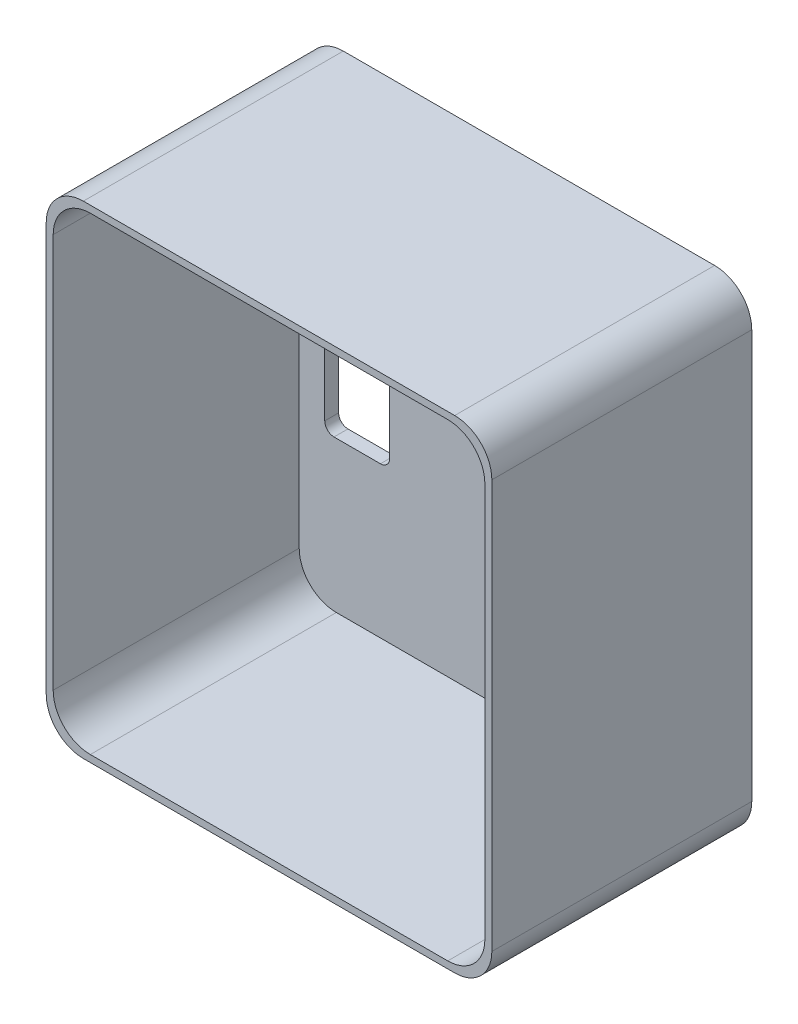
SolidWorks part; units mm, degrees
ref_plane "Front Plane" through (0, 0, 0) normal (0, 0, 1) x (1, 0, 0)
ref_plane "Top Plane" through (0, 0, 0) normal (0, 1, 0) x (1, 0, 0)
ref_plane "Right Plane" through (0, 0, 0) normal (1, 0, 0) x (0, 0, -1)
sketch "Sketch1" plane through (0, 0, 0) normal (0, 0, 1) x (1, 0, 0)
  line L1 (-20, 26) -> (20, 26)
  line L2 (-24, 22) -> (-24, -22)
  line L3 (-20, -26) -> (20, -26)
  line L4 (24, 22) -> (24, -22)
  line L5 (-24, 26) -> (24, -26) construction
  line L6 (-24, -26) -> (24, 26) construction
  arc A0 (20, -26) -> (24, -22) centre (20, -22) ccw
  arc A1 (-24, -22) -> (-20, -26) centre (-20, -22) ccw
  arc A2 (24, 22) -> (20, 26) centre (20, 22) ccw
  arc A3 (-20, 26) -> (-24, 22) centre (-20, 22) ccw
  point P0 (0, 0)
  dimension "D3" = 4
  dimension "D1" = 52
  dimension "D2" = 48
extrude "Boss-Extrude1" add sketch "Sketch1" along normal blind 28
sketch "Sketch2" plane through (0, 0, 28) normal (0, 0, 1) x (1, 0, 0)
  line L1 (-19.25, 25.25) -> (19.25, 25.25)
  line L2 (-23.25, 21.25) -> (-23.25, -21.25)
  line L3 (-19.25, -25.25) -> (19.25, -25.25)
  line L4 (23.25, 21.25) -> (23.25, -21.25)
  line L5 (-23.25, 25.25) -> (23.25, -25.25) construction
  line L6 (-23.25, -25.25) -> (23.25, 25.25) construction
  arc A0 (-23.25, -21.25) -> (-19.25, -25.25) centre (-19.25, -21.25) ccw
  arc A1 (19.25, -25.25) -> (23.25, -21.25) centre (19.25, -21.25) ccw
  arc A2 (23.25, 21.25) -> (19.25, 25.25) centre (19.25, 21.25) ccw
  arc A3 (-19.25, 25.25) -> (-23.25, 21.25) centre (-19.25, 21.25) ccw
  point P0 (0, 0)
  dimension "D3" = 4
  dimension "D1" = 50.5
  dimension "D2" = 46.5
extrude "Cut-Extrude1" cut sketch "Sketch2" against normal blind 26.5
sketch "Sketch3" plane through (0, 0, 1.5) normal (0, 0, 1) x (1, 0, 0)
  line L1 (-19.5, 9) -> (-14.5, 9)
  line L2 (-20.5, 8) -> (-20.5, -8)
  line L3 (-19.5, -9) -> (-14.5, -9)
  line L4 (-13.5, 8) -> (-13.5, -8)
  line L5 (-20.5, 9) -> (-13.5, -9) construction
  line L6 (-20.5, -9) -> (-13.5, 9) construction
  arc A0 (-20.5, -8) -> (-19.5, -9) centre (-19.5, -8) ccw
  arc A1 (-14.5, -9) -> (-13.5, -8) centre (-14.5, -8) ccw
  arc A2 (-13.5, 8) -> (-14.5, 9) centre (-14.5, 8) ccw
  arc A3 (-19.5, 9) -> (-20.5, 8) centre (-19.5, 8) ccw
  point P0 (-17, 0)
  dimension "D4" = 1
  dimension "D1" = 18
  dimension "D2" = 7
  dimension "D3" = 17
extrude "Cut-Extrude2" cut sketch "Sketch3" against normal through all
